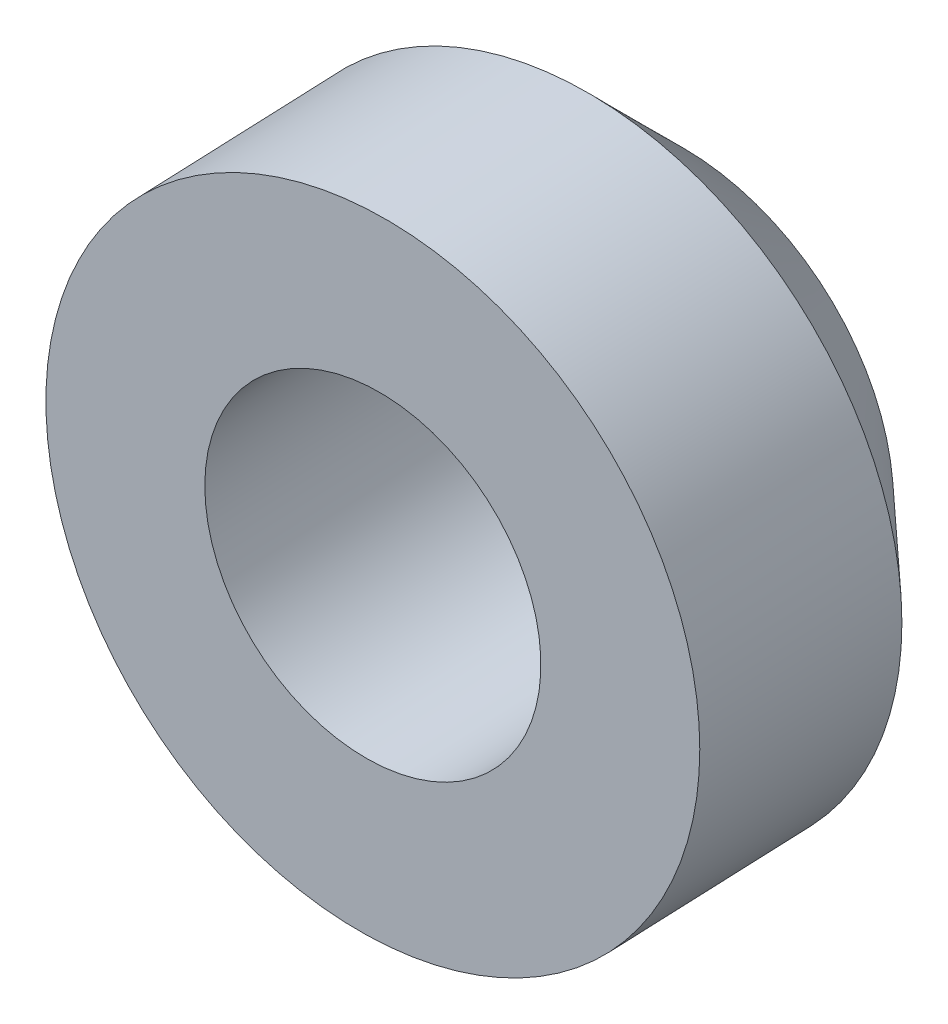
SolidWorks part; units mm, degrees
material "6061-T6 (SS)"
ref_plane "Top" through (0, 0, 0) normal (0, 0, 1) x (1, 0, 0)
ref_plane "Right" through (0, 0, 0) normal (0, 1, 0) x (1, 0, 0)
ref_plane "Front" through (0, 0, 0) normal (1, 0, 0) x (0, 0, -1)
ref_plane "Ball Joint Axis Plane" through (14.2345, 0, 353.9675) normal (0.0402, 0, 0.9992) x (0.9992, 0, -0.0402)
ref_plane "Ball Joint 1/2 Thickness" through (14.4259, 0, 358.7262) normal (0.0402, 0, 0.9992) x (0.9992, 0, -0.0402)
ref_plane "Midplane" through (1571.6322, 520.7, 291.338) normal (0.9992, 0, -0.0402) x (-0.0402, 0, -0.9992)
sketch "Sketch1" plane through (1571.6322, 520.7, 291.338) normal (0.9992, 0, -0.0402) x (-0.0402, 0, -0.9992)
  line L1 (-11.1125, -41.3639) -> (-11.1125, -34.8361) construction
  line L2 (-4.7625, -502.1199) -> (-4.7625, -539.2801) construction
  line L3 (-11.1125, -41.3639) -> (-11.1125, -34.8361) construction
  line L5 (-11.1125, -38.1) -> (-4.7625, -38.1)
  line L6 (-4.7625, -38.1) -> (-4.7625, -33.8455)
  line L7 (-4.7625, -33.8455) -> (-6.858, -31.75)
  line L8 (-6.858, -31.75) -> (-11.1125, -31.75)
  line L9 (-11.1125, -31.75) -> (-11.1125, -38.1)
  line L10 (-11.1125, -31.75) -> (-11.1125, -38.1)
  dimension "D1" = 45
  dimension "D2" = 4.2545
  dimension "D3" = 6.35
revolve "Revolve1" add sketch "Sketch1" angle 360 about L5
hole_wizard "1/4 Clearance Hole1" positions "Sketch2" profile "Sketch3" hole size "1/4" standard "ANSI Inch" end condition through all
sketch "Sketch2" plane through (14.4259, 0, 358.7262) normal (-0.0402, 0, -0.9992) x (-0.9992, 0, 0.0402)
  point P0 (-1558.6565, 482.6)
sketch "Sketch3" plane through (1571.8236, 482.6, 296.0967) normal (0, 1, 0) x (-0.9992, 0, 0.0402)
  line L0 (0, 0) -> (0, 6.8599)
  line L1 (0, 6.8599) -> (3.2639, 6.8599)
  line L2 (3.2639, 6.8599) -> (3.2639, 0)
  line L5 (3.2639, 0) -> (0, 0)
  line L11 (0, -6.35) -> (0, 107.95) construction
  dimension "Thru Hole Dia." = 6.5278
  dimension "Thru Hole Depth" = 6.8599
sketch "Sketch4" plane through (14.681, 0, 365.071) normal (0.0402, 0, 0.9992) x (0.9992, 0, -0.0402)
  circle A0 centre (1558.6565, 482.6) radius 3.2639 construction
  circle A1 centre (1558.6565, 482.6) radius 6.35
  circle A2 centre (1558.6565, 482.6) radius 6.35
  circle A3 centre (1558.6565, 482.6) radius 3.2639
  dimension "D1" = 0
extrude "Boss-Extrude1" [suppressed] add sketch "Sketch4" along normal blind 1.27
